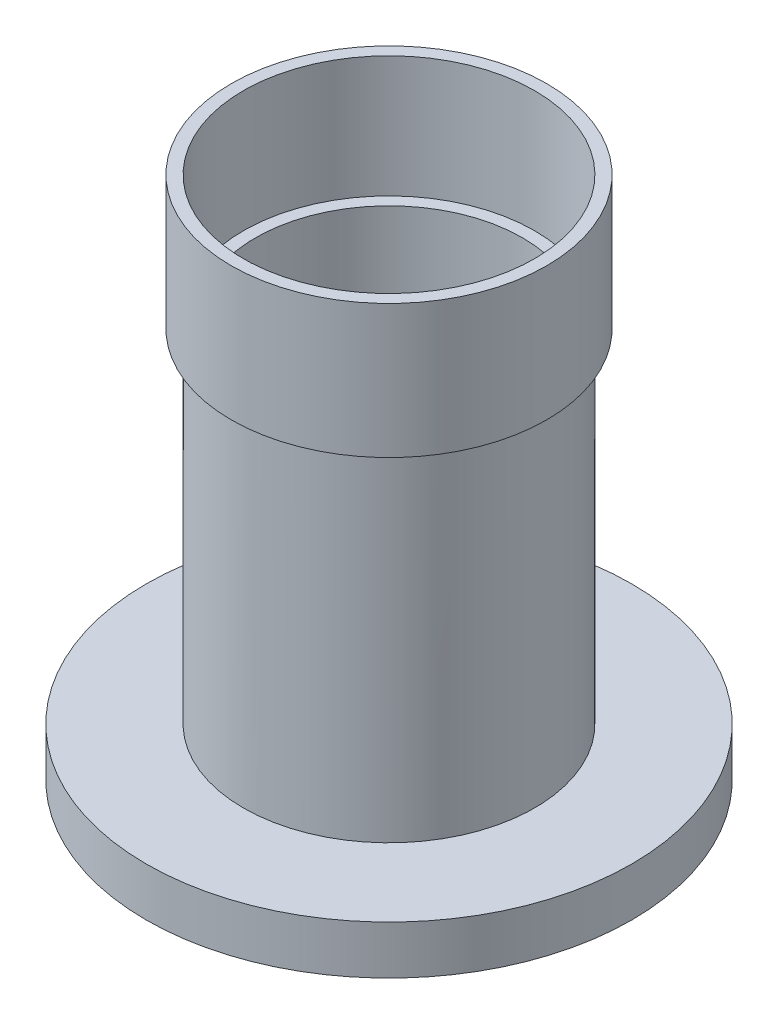
SolidWorks part; units mm, degrees
ref_plane "Front Plane" through (0, 0, 0) normal (0, 0, 1) x (1, 0, 0)
ref_plane "Top Plane" through (0, 0, 0) normal (0, 1, 0) x (1, 0, 0)
ref_plane "Right Plane" through (0, 0, 0) normal (1, 0, 0) x (0, 0, -1)
sketch "Sketch1" plane through (0, 0, 0) normal (0, 1, 0) x (1, 0, 0)
  circle A0 centre (0, 0) radius 31.75
  dimension "D1" = 63.5
extrude "Boss-Extrude1" add sketch "Sketch1" along normal blind 6.35
sketch "Sketch2" plane through (0, 0, 0) normal (0, 0, 1) x (1, 0, 0)
  line L0 (0, -26.0675) -> (0, 48.7435) construction
  line L2 (31.75, 6.35) -> (-31.75, 6.35) construction
  line L3 (19.05, 6.35) -> (19.05, 51.1175)
  line L4 (19.05, 51.1175) -> (20.6375, 51.1175)
  line L5 (20.6375, 51.1175) -> (20.6375, 68.58)
  line L6 (20.6375, 68.58) -> (19.05, 68.58)
  line L7 (19.05, 68.58) -> (19.05, 52.705)
  line L8 (19.05, 52.705) -> (17.4625, 52.705)
  line L9 (17.4625, 52.705) -> (17.4625, 6.35)
  line L10 (17.4625, 6.35) -> (19.05, 6.35)
  dimension "D1" = 34.925
  dimension "D2" = 38.1
  dimension "D3" = 38.1
  dimension "D4" = 41.275
  dimension "D5" = 1.5875
  dimension "D6" = 46.355
  dimension "D7" = 15.875
revolve "Revolve1" add sketch "Sketch2" angle 360 about L0
